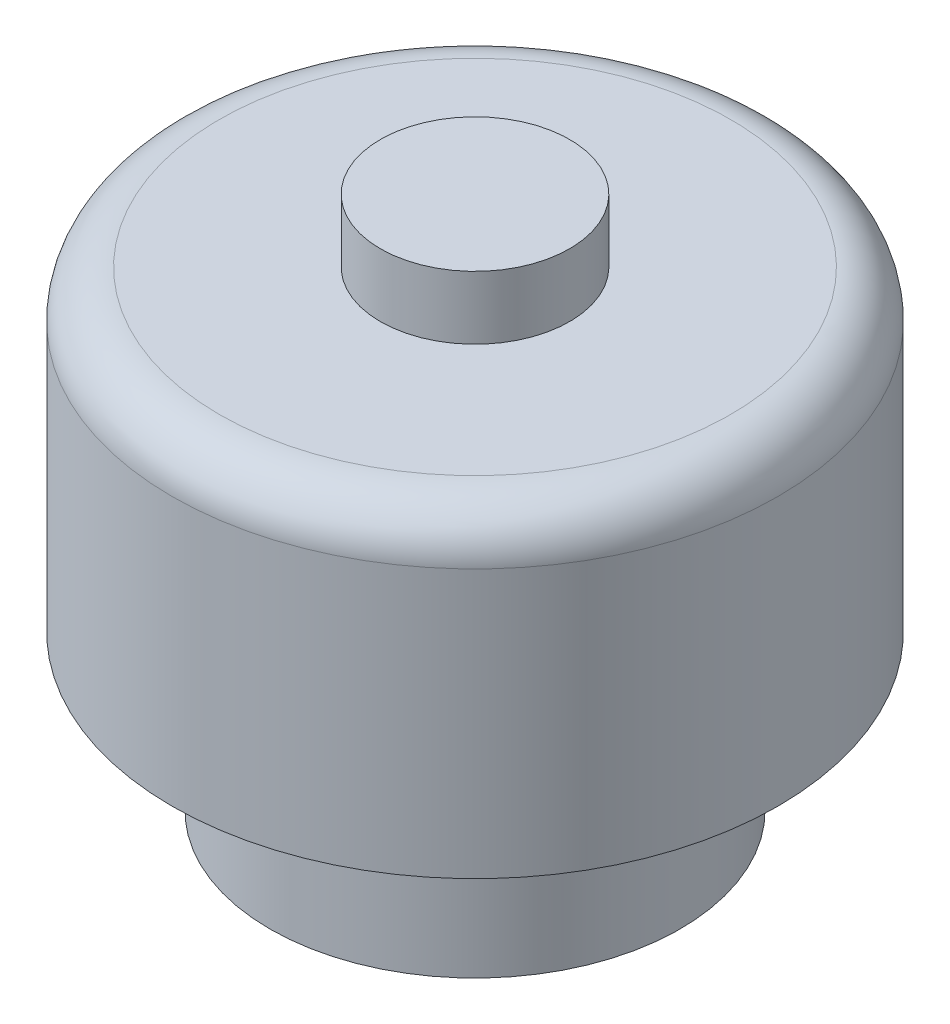
SolidWorks part; units mm, degrees
ref_plane "Front Plane" through (0, 0, 0) normal (0, 0, 1) x (1, 0, 0)
ref_plane "Top Plane" through (0, 0, 0) normal (0, 1, 0) x (1, 0, 0)
ref_plane "Right Plane" through (0, 0, 0) normal (1, 0, 0) x (0, 0, -1)
sketch "Sketch1" plane through (0, 0, 0) normal (0, 1, 0) x (1, 0, 0)
  circle A0 centre (0, 0) radius 3.25
  dimension "D1" = 6.5
extrude "Boss-Extrude1" add sketch "Sketch1" along normal blind 2.46 contours A0
sketch "Sketch2" plane through (0, 0, 0) normal (0, -1, 0) x (1, 0, 0)
  circle A1 centre (0, 0) radius 1.75
  dimension "D1" = 3.5
extrude "Cut-Extrude1" cut sketch "Sketch2" against normal blind 2.5
sketch "Sketch6" plane through (0, 2.46, 0) normal (0, 1, 0) x (1, 0, 0)
  circle A0 centre (0, 0) radius 4.8
  dimension "D1" = 9.6
extrude "Boss-Extrude2" add sketch "Sketch6" along normal blind 5 contours A0
fillet "Fillet2" radius 0.75 1 edges at (0, 7.46, 4.8)
sketch "Sketch7" plane through (0, 7.46, 0) normal (0, 1, 0) x (1, 0, 0)
  circle A0 centre (0, 0) radius 1.5
  dimension "D1" = 3
extrude "Boss-Extrude3" add sketch "Sketch7" along normal blind 1
